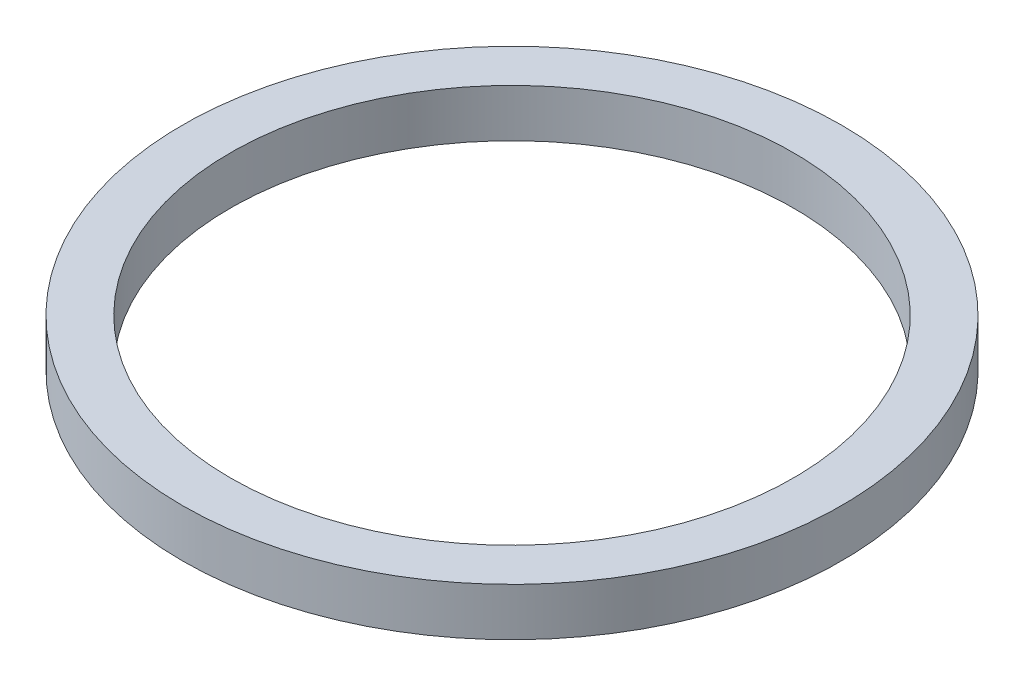
SolidWorks part; units mm, degrees
ref_plane "Front Plane" through (0, 0, 0) normal (0, 0, 1) x (1, 0, 0)
ref_plane "Top Plane" through (0, 0, 0) normal (0, 1, 0) x (1, 0, 0)
ref_plane "Right Plane" through (0, 0, 0) normal (1, 0, 0) x (0, 0, -1)
sketch "Sketch1" plane through (0, 0, 0) normal (0, 1, 0) x (1, 0, 0)
  circle A0 centre (0, 0) radius 13.75
  circle A1 centre (0, 0) radius 11.75
  dimension "D1" = 27.5
  dimension "D2" = 2
extrude "Boss-Extrude1" add sketch "Sketch1" along normal blind 2
